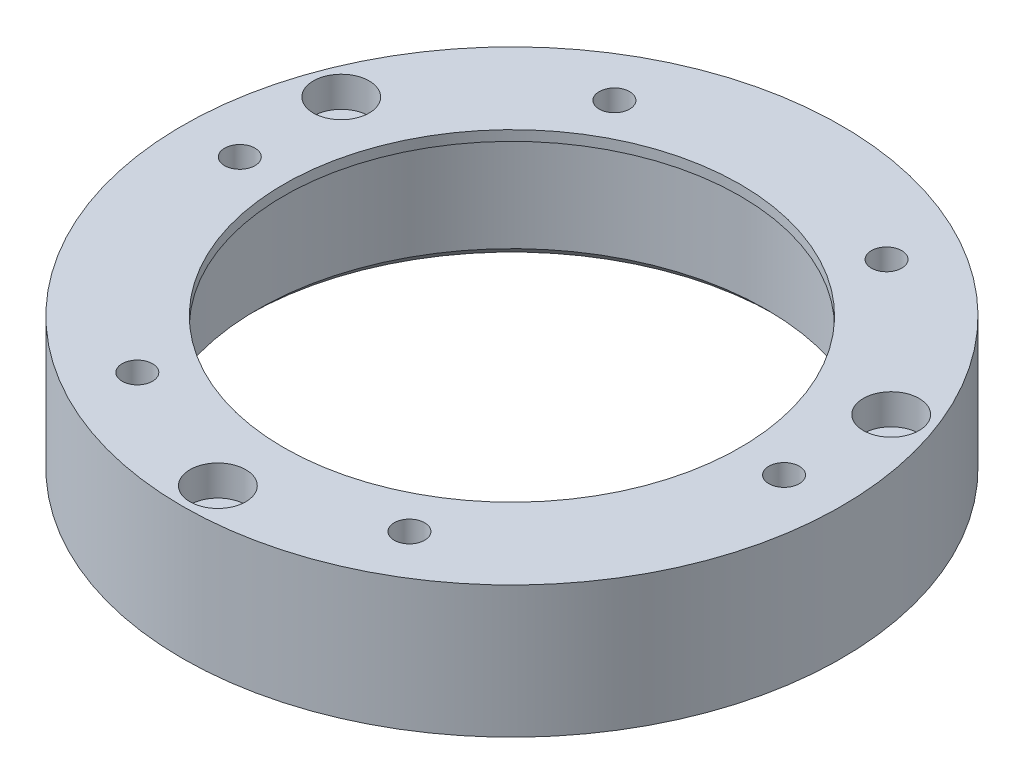
SolidWorks part; units mm, degrees
ref_plane "Front Plane" through (0, 0, 0) normal (0, 0, 1) x (1, 0, 0)
ref_plane "Top Plane" through (0, 0, 0) normal (0, 1, 0) x (1, 0, 0)
ref_plane "Right Plane" through (0, 0, 0) normal (1, 0, 0) x (0, 0, -1)
sketch "Sketch1" plane through (0, 0, 0) normal (0, 1, 0) x (1, 0, 0)
  circle A0 centre (0, 0) radius 32.5
  circle A1 centre (0, 0) radius 25.1
  dimension "D1" = 65
  dimension "D2" = 50.2
extrude "Boss-Extrude1" add sketch "Sketch1" along normal blind 13
sketch "Sketch2" plane through (0, 13, 0) normal (0, 1, 0) x (1, 0, 0)
  circle A0 centre (0, 0) radius 22.5
  circle A1 centre (0, 0) radius 25.1 construction
  circle A2 centre (0, 0) radius 25.1
  dimension "D1" = 45
extrude "Boss-Extrude2" add sketch "Sketch2" against normal blind 1
sketch "Sketch3" plane through (0, 0, 0) normal (0, -1, 0) x (-1, 0, 0)
  line L0 (0, 0) -> (0, -29) construction
  line L1 (0, 0) -> (-27.1153, 10.2839) construction
  circle A0 centre (0, -29) radius 1.5
  circle A1 centre (-27.1153, 10.2839) radius 1.5
  circle A2 centre (27.1153, 10.2839) radius 1.5
  point P5 (0, 0)
  point P10 (0, 0)
  point P12 (0, 0)
  dimension "D2" = 3
  dimension "D1" = 29
  dimension "D4" = 110.77
  dimension "D6" = 0
  dimension "D3" = 2
  dimension "D5" = 2
extrude "Cut-Extrude1" cut sketch "Sketch3" against normal through all
chamfer "Chamfer1" distance 1 angle 45 1 edges at (0, 0, 25.1)
sketch "Sketch4" plane through (0, 13, 0) normal (0, 1, 0) x (1, 0, 0)
  circle A0 centre (-27.1153, 10.2839) radius 2.75
  circle A1 centre (27.1153, 10.2839) radius 2.75
  circle A2 centre (0, -29) radius 2.75
  dimension "D1" = 5.5
  dimension "D2" = 5.5
  dimension "D3" = 5.5
extrude "Cut-Extrude2" cut sketch "Sketch4" against normal blind 3
sketch "Sketch5" plane through (0, 13, 0) normal (0, 1, 0) x (1, 0, 0)
  circle A0 centre (13.6418, 23.3002) radius 1.5
  circle A1 centre (26.9995, -0.1641) radius 1.5
  circle A2 centre (13.3577, -23.4643) radius 1.5
  circle A3 centre (-13.6418, -23.3002) radius 1.5
  circle A4 centre (-26.9995, 0.1641) radius 1.5
  circle A5 centre (-13.3577, 23.4643) radius 1.5
  point P4 (0, 0)
  point P5 (13.3577, 23.4643)
  point P15 (0, 0)
  dimension "D2" = 3
  dimension "D1" = 27
  dimension "D3" = 6
extrude "Cut-Extrude3" cut sketch "Sketch5" against normal blind 10
